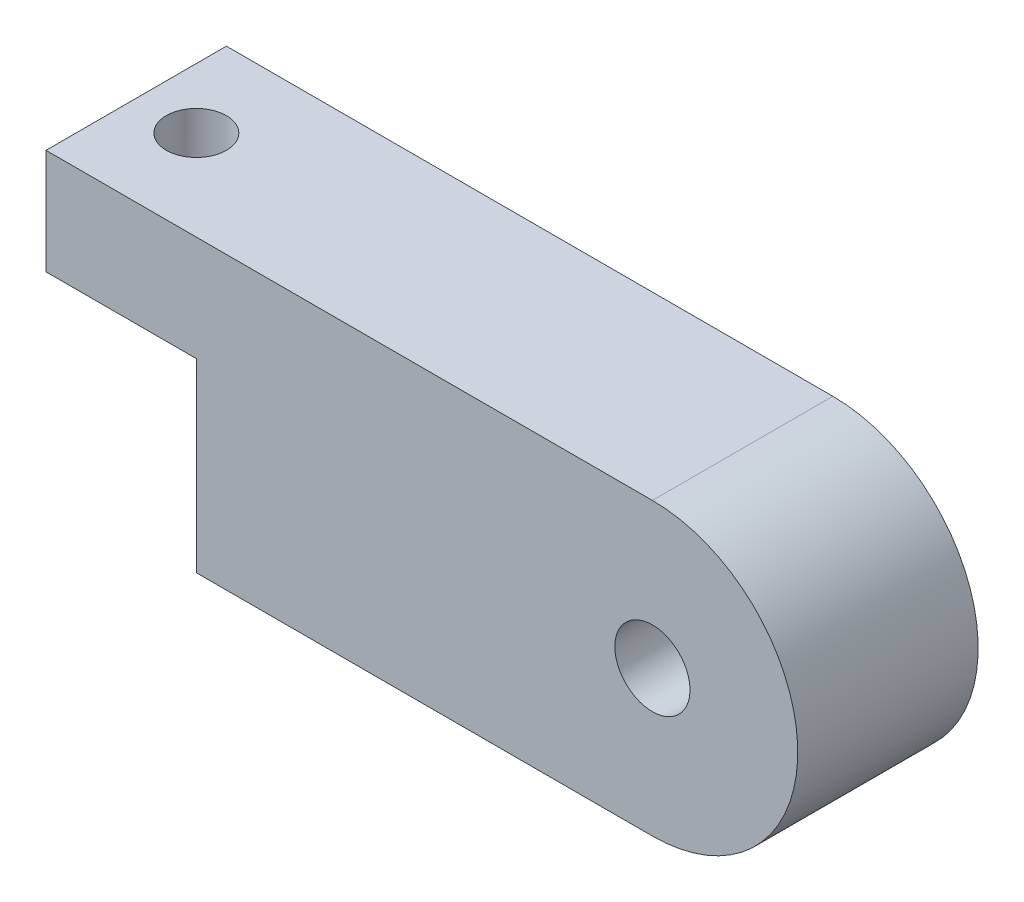
SolidWorks part; units mm, degrees
ref_plane "Front Plane" through (0, 0, 0) normal (0, 0, 1) x (1, 0, 0)
ref_plane "Top Plane" through (0, 0, 0) normal (0, 1, 0) x (1, 0, 0)
ref_plane "Right Plane" through (0, 0, 0) normal (1, 0, 0) x (0, 0, -1)
sketch "Sketch2" plane through (0, 0, 0) normal (0, 0, 1) x (1, 0, 0)
  line L1 (0, 0) -> (200, 0)
  line L2 (0, 0) -> (0, -96.6667)
  line L3 (0, -96.6667) -> (200, -96.6667)
  line L4 (200, 0) -> (200, -96.6667)
  dimension "D1" = 200
extrude "Boss-Extrude2" add sketch "Sketch2" against normal blind 60
fillet "Fillet12" radius 48.3333 4 edges at (200, -48.3333, -60) (200, -48.3333, 0) (200, 0, -30) (200, -96.6667, -30)
sketch "Sketch6" plane through (0, 0, -60) normal (0, 0, -1) x (-1, 0, 0)
  circle A0 centre (-151.6667, -48.3333) radius 12.5
  dimension "25" = 25
extrude "Cut-Extrude3" cut sketch "Sketch6" against normal through all
sketch "Sketch8" plane through (0, 0, 0) normal (-1, 0, 0) x (0, 0, 1)
  line L0 (-60, 0) -> (-60, -96.6667) construction
  line L1 (-60, 0) -> (0, 0)
  line L2 (-60, 0) -> (-60, -35)
  line L3 (-60, -35) -> (0, -35)
  line L4 (0, 0) -> (0, -35)
  line L5 (-60, 0) -> (0, 0) construction
  line L6 (0, 0) -> (0, -96.6667) construction
  dimension "D1" = 35
extrude "Boss-Extrude3" add sketch "Sketch8" along normal blind 50
sketch "Sketch10" plane through (0, 0, 0) normal (0, 1, 0) x (1, 0, 0)
  line L0 (-50, 0) -> (-50, 60) construction
  circle A0 centre (-30, 30) radius 10
  dimension "D1" = 20
  dimension "D2" = 20
extrude "Cut-Extrude4" cut sketch "Sketch10" against normal blind 50
